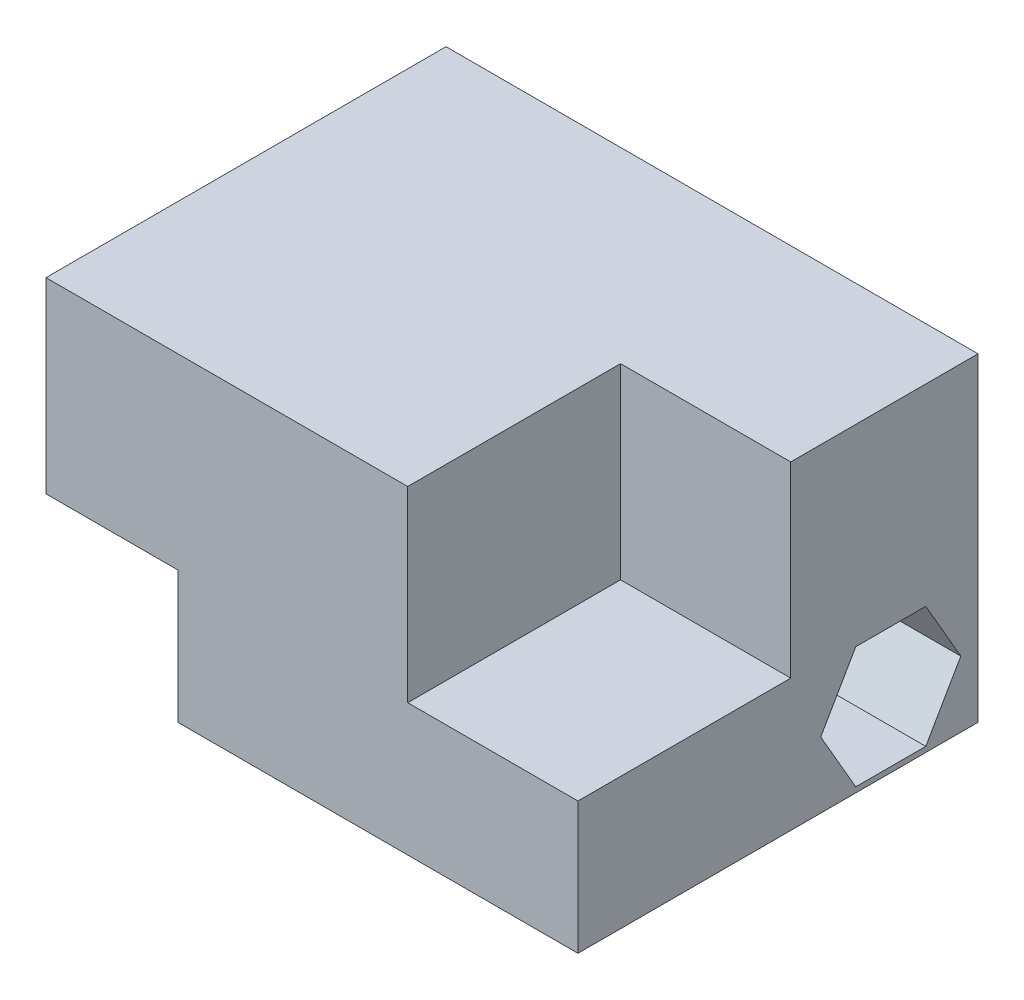
SolidWorks part; units mm, degrees
ref_plane "Alzado" through (0, 0, 0) normal (0, 0, 1) x (1, 0, 0)
ref_plane "Planta" through (0, 0, 0) normal (0, 1, 0) x (1, 0, 0)
ref_plane "Vista lateral" through (0, 0, 0) normal (1, 0, 0) x (0, 0, -1)
sketch "Croquis1" plane through (0, 0, 0) normal (0, 0, 1) x (1, 0, 0)
  line L0 (0, 0) -> (0, 15)
  line L1 (0, 15) -> (-25, 15)
  line L2 (-25, 15) -> (-25, 6.2)
  line L3 (-25, 6.2) -> (-18.8, 6.2)
  line L4 (-18.8, 6.2) -> (-18.8, 0)
  line L5 (-18.8, 0) -> (0, 0)
  dimension "D1" = 15
  dimension "D2" = 25
  dimension "D3" = 6.2
extrude "Saliente-Extruir1" add sketch "Croquis1" along normal blind 8.8
sketch "Croquis2" plane through (0, 0, 8.8) normal (0, 0, 1) x (1, 0, 0)
  line L0 (-8, 15) -> (-8, 6.2)
  line L1 (-8, 6.2) -> (0, 6.2)
  line L2 (0, 0) -> (0, 15) construction
  line L3 (0, 6.2) -> (0, 0)
  line L4 (0, 0) -> (-8, 0)
  line L6 (-18.8, 0) -> (0, 0)
  line L7 (0, 0) -> (0, 15)
  line L8 (0, 15) -> (-25, 15)
  line L9 (-25, 15) -> (-25, 6.2)
  line L10 (-25, 6.2) -> (-18.8, 6.2)
  line L11 (-18.8, 6.2) -> (-18.8, 0)
  line L12 (-18.8, 0) -> (-8, 0)
  line L14 (-8, 15) -> (-25, 15)
  line L15 (-25, 15) -> (-25, 6.2)
  line L16 (-25, 6.2) -> (-18.8, 6.2)
  line L17 (-18.8, 6.2) -> (-18.8, 0)
  dimension "D2" = 10.8
  dimension "D1" = 0
extrude "Saliente-Extruir2" add sketch "Croquis2" along normal blind 10
sketch "Croquis3" plane through (0, 0, 0) normal (1, 0, 0) x (0, 0, -1)
  line L0 (-18.8, 3.1) -> (-8.8, 3.1) construction
  line L1 (-18.8, 0) -> (-18.8, 6.2) construction
  line L2 (-8.8, 3.1) -> (-4.1, 3.1) construction
  line L3 (-4.1, 3.1) -> (-8.8, 6.2) construction
  line L4 (-8.8, 6.2) -> (-8.8, 3.1) construction
  circle A0 centre (-4.1, 3.1) radius 1.6
  dimension "D2" = 3.2
  dimension "D1" = 4.7
extrude "Cortar-Extruir1" cut sketch "Croquis3" against normal up to next
sketch "Croquis4" plane through (0, 0, 0) normal (1, 0, 0) x (0, 0, -1)
  line L1 (-0.8091, 3.1) -> (-2.4546, 5.95)
  line L2 (-2.4546, 5.95) -> (-5.7454, 5.95)
  line L3 (-5.7454, 5.95) -> (-7.3909, 3.1)
  line L4 (-7.3909, 3.1) -> (-5.7454, 0.25)
  line L5 (-5.7454, 0.25) -> (-2.4546, 0.25)
  line L6 (-2.4546, 0.25) -> (-0.8091, 3.1)
  circle A0 centre (-4.1, 3.1) radius 2.85 construction
  dimension "D1" = 5.7
extrude "Cortar-Extruir2" cut sketch "Croquis4" against normal offset from surface (11.8 mm away) 7 up to face at (-18.8, 3.1, 2.5)
